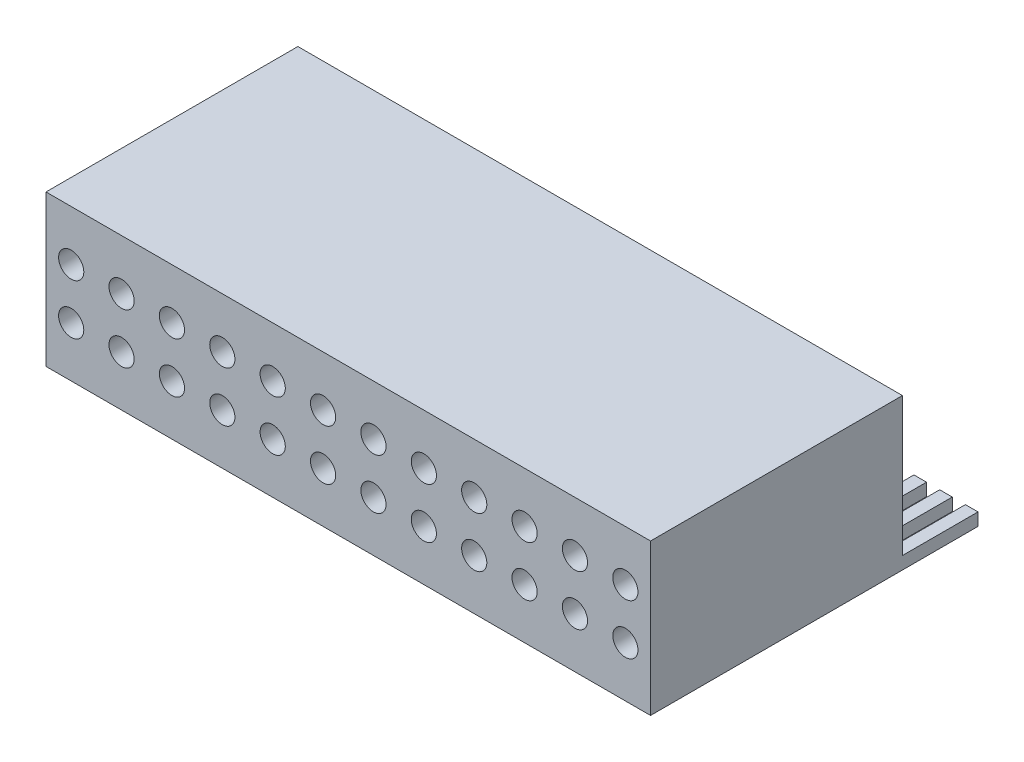
SolidWorks part; units mm, degrees
ref_plane "Front Plane" through (0, 0, 0) normal (0, 0, 1) x (1, 0, 0)
ref_plane "Top Plane" through (0, 0, 0) normal (0, 1, 0) x (1, 0, 0)
ref_plane "Right Plane" through (0, 0, 0) normal (1, 0, 0) x (0, 0, -1)
sketch "Sketch2" plane through (0, 0, 0) normal (0, 0, 1) x (1, 0, 0)
  line L1 (0, 0) -> (24, 0)
  line L2 (0, 0) -> (0, 6)
  line L3 (0, 6) -> (24, 6)
  line L4 (24, 0) -> (24, 6)
  dimension "D1" = 24
  dimension "D2" = 6
extrude "Boss-Extrude1" add sketch "Sketch2" along normal blind 10
sketch "Sketch3" plane through (0, 0, 10) normal (0, 0, 1) x (1, 0, 0)
  line L1 (0, 6) -> (0, 0) construction
  line L2 (24, 0) -> (24, 6) construction
  line L3 (0, 3) -> (24, 3) construction
  line L8 (-1, 2) -> (23, 2) construction
  line L9 (1, 6) -> (1, 0) construction
  line L10 (1, 2) -> (3, 2) construction
  circle A24 centre (1, 2) radius 0.5
  circle A25 centre (3, 2) radius 0.5
  circle A26 centre (5, 2) radius 0.5
  circle A27 centre (7, 2) radius 0.5
  circle A28 centre (9, 2) radius 0.5
  circle A29 centre (11, 2) radius 0.5
  circle A30 centre (13, 2) radius 0.5
  circle A31 centre (15, 2) radius 0.5
  circle A32 centre (17, 2) radius 0.5
  circle A33 centre (19, 2) radius 0.5
  circle A34 centre (21, 2) radius 0.5
  circle A35 centre (23, 2) radius 0.5
  circle A36 centre (23, 4) radius 0.5
  circle A37 centre (21, 4) radius 0.5
  circle A38 centre (19, 4) radius 0.5
  circle A39 centre (17, 4) radius 0.5
  circle A40 centre (15, 4) radius 0.5
  circle A41 centre (13, 4) radius 0.5
  circle A42 centre (11, 4) radius 0.5
  circle A43 centre (9, 4) radius 0.5
  circle A44 centre (7, 4) radius 0.5
  circle A45 centre (5, 4) radius 0.5
  circle A46 centre (3, 4) radius 0.5
  circle A47 centre (1, 4) radius 0.5
extrude "Cut-Extrude1" cut sketch "Sketch3" against normal blind 5
sketch "Sketch4" plane through (0, 0, 0) normal (0, -1, 0) x (-1, 0, 0)
  line L96 (0, 0) -> (0, 3)
  line L98 (0, 3) -> (-0.5, 3)
  line L99 (-0.5, 3) -> (-0.5, 0)
  line L100 (-24, 0) -> (0, 0) construction
  line L101 (-0.5, 0) -> (0, 0)
  line L102 (-1.0217, 0) -> (-1.0217, 3)
  line L103 (-1.0217, 3) -> (-1.5217, 3)
  line L104 (-1.5217, 3) -> (-1.5217, 0)
  line L105 (-1.5217, 0) -> (-1.0217, 0)
  line L106 (-2.0435, 0) -> (-2.0435, 3)
  line L107 (-2.0435, 3) -> (-2.5435, 3)
  line L108 (-2.5435, 3) -> (-2.5435, 0)
  line L109 (-2.5435, 0) -> (-2.0435, 0)
  line L110 (-3.0652, 0) -> (-3.0652, 3)
  line L111 (-3.0652, 3) -> (-3.5652, 3)
  line L112 (-3.5652, 3) -> (-3.5652, 0)
  line L113 (-3.5652, 0) -> (-3.0652, 0)
  line L114 (-4.087, 0) -> (-4.087, 3)
  line L115 (-4.087, 3) -> (-4.587, 3)
  line L116 (-4.587, 3) -> (-4.587, 0)
  line L117 (-4.587, 0) -> (-4.087, 0)
  line L118 (-5.1087, 0) -> (-5.1087, 3)
  line L119 (-5.1087, 3) -> (-5.6087, 3)
  line L120 (-5.6087, 3) -> (-5.6087, 0)
  line L121 (-5.6087, 0) -> (-5.1087, 0)
  line L122 (-6.1304, 0) -> (-6.1304, 3)
  line L123 (-6.1304, 3) -> (-6.6304, 3)
  line L124 (-6.6304, 3) -> (-6.6304, 0)
  line L125 (-6.6304, 0) -> (-6.1304, 0)
  line L126 (-7.1522, 0) -> (-7.1522, 3)
  line L127 (-7.1522, 3) -> (-7.6522, 3)
  line L128 (-7.6522, 3) -> (-7.6522, 0)
  line L129 (-7.6522, 0) -> (-7.1522, 0)
  line L130 (-8.1739, 0) -> (-8.1739, 3)
  line L131 (-8.1739, 3) -> (-8.6739, 3)
  line L132 (-8.6739, 3) -> (-8.6739, 0)
  line L133 (-8.6739, 0) -> (-8.1739, 0)
  line L134 (-9.1957, 0) -> (-9.1957, 3)
  line L135 (-9.1957, 3) -> (-9.6957, 3)
  line L136 (-9.6957, 3) -> (-9.6957, 0)
  line L137 (-9.6957, 0) -> (-9.1957, 0)
  line L138 (-10.2174, 0) -> (-10.2174, 3)
  line L139 (-10.2174, 3) -> (-10.7174, 3)
  line L140 (-10.7174, 3) -> (-10.7174, 0)
  line L141 (-10.7174, 0) -> (-10.2174, 0)
  line L142 (-11.2391, 0) -> (-11.2391, 3)
  line L143 (-11.2391, 3) -> (-11.7391, 3)
  line L144 (-11.7391, 3) -> (-11.7391, 0)
  line L145 (-11.7391, 0) -> (-11.2391, 0)
  line L146 (-12.2609, 0) -> (-12.2609, 3)
  line L147 (-12.2609, 3) -> (-12.7609, 3)
  line L148 (-12.7609, 3) -> (-12.7609, 0)
  line L149 (-12.7609, 0) -> (-12.2609, 0)
  line L150 (-13.2826, 0) -> (-13.2826, 3)
  line L151 (-13.2826, 3) -> (-13.7826, 3)
  line L152 (-13.7826, 3) -> (-13.7826, 0)
  line L153 (-13.7826, 0) -> (-13.2826, 0)
  line L154 (-14.3043, 0) -> (-14.3043, 3)
  line L155 (-14.3043, 3) -> (-14.8043, 3)
  line L156 (-14.8043, 3) -> (-14.8043, 0)
  line L157 (-14.8043, 0) -> (-14.3043, 0)
  line L158 (-15.3261, 0) -> (-15.3261, 3)
  line L159 (-15.3261, 3) -> (-15.8261, 3)
  line L160 (-15.8261, 3) -> (-15.8261, 0)
  line L161 (-15.8261, 0) -> (-15.3261, 0)
  line L162 (-16.3478, 0) -> (-16.3478, 3)
  line L163 (-16.3478, 3) -> (-16.8478, 3)
  line L164 (-16.8478, 3) -> (-16.8478, 0)
  line L165 (-16.8478, 0) -> (-16.3478, 0)
  line L166 (-17.3696, 0) -> (-17.3696, 3)
  line L167 (-17.3696, 3) -> (-17.8696, 3)
  line L168 (-17.8696, 3) -> (-17.8696, 0)
  line L169 (-17.8696, 0) -> (-17.3696, 0)
  line L170 (-18.3913, 0) -> (-18.3913, 3)
  line L171 (-18.3913, 3) -> (-18.8913, 3)
  line L172 (-18.8913, 3) -> (-18.8913, 0)
  line L173 (-18.8913, 0) -> (-18.3913, 0)
  line L174 (-19.413, 0) -> (-19.413, 3)
  line L175 (-19.413, 3) -> (-19.913, 3)
  line L176 (-19.913, 3) -> (-19.913, 0)
  line L177 (-19.913, 0) -> (-19.413, 0)
  line L178 (-20.4348, 0) -> (-20.4348, 3)
  line L179 (-20.4348, 3) -> (-20.9348, 3)
  line L180 (-20.9348, 3) -> (-20.9348, 0)
  line L181 (-20.9348, 0) -> (-20.4348, 0)
  line L182 (-21.4565, 0) -> (-21.4565, 3)
  line L183 (-21.4565, 3) -> (-21.9565, 3)
  line L184 (-21.9565, 3) -> (-21.9565, 0)
  line L185 (-21.9565, 0) -> (-21.4565, 0)
  line L186 (-22.4783, 0) -> (-22.4783, 3)
  line L187 (-22.4783, 3) -> (-22.9783, 3)
  line L188 (-22.9783, 3) -> (-22.9783, 0)
  line L189 (-22.9783, 0) -> (-22.4783, 0)
  line L190 (-23.5, 0) -> (-23.5, 3)
  line L191 (-23.5, 3) -> (-24, 3)
  line L192 (-24, 3) -> (-24, 0)
  line L193 (-24, 0) -> (-23.5, 0)
  line L194 (0, 0) -> (-1.0217, 0) construction
  dimension "D1" = 1.0217
extrude "Boss-Extrude2" add sketch "Sketch4" against normal blind 0.5
